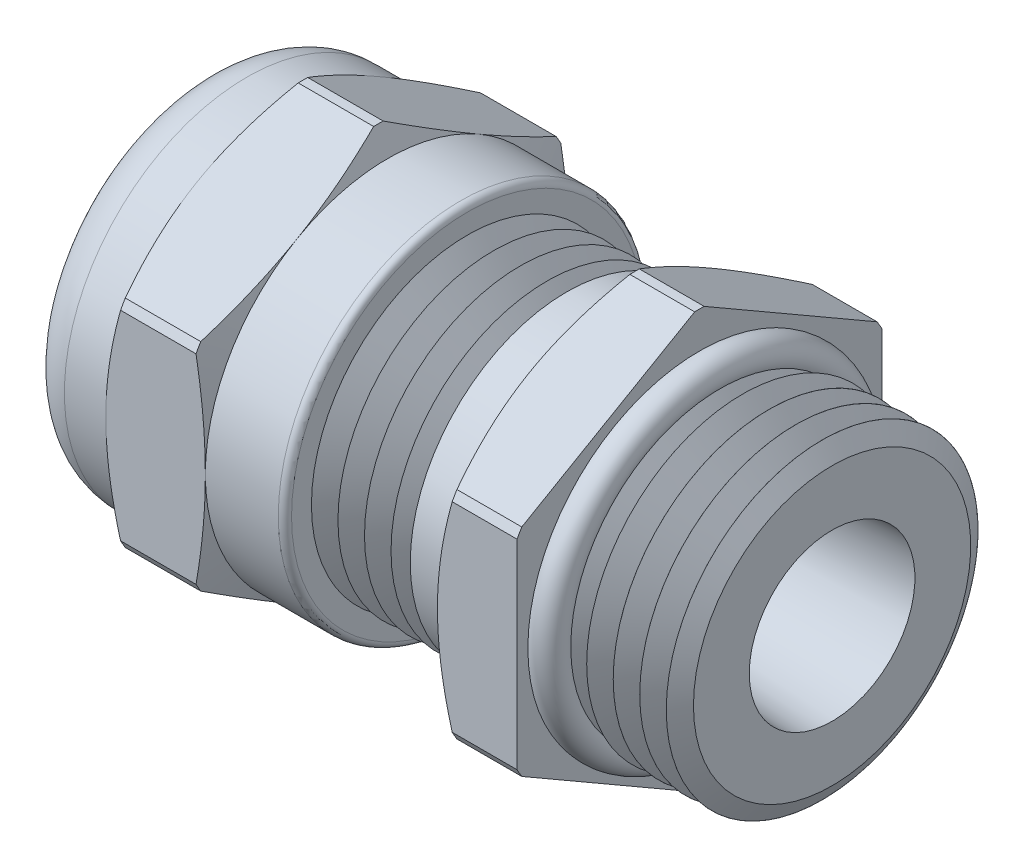
SolidWorks part; units mm, degrees
ref_plane "Front Plane" through (0, 0, 0) normal (0, 0, 1) x (1, 0, 0)
ref_plane "Top Plane" through (0, 0, 0) normal (0, 1, 0) x (1, 0, 0)
ref_plane "Right Plane" through (0, 0, 0) normal (1, 0, 0) x (0, 0, -1)
sketch "Sketch2" plane through (0, 0, 0) normal (0, 0, 1) x (1, 0, 0)
  line L0 (-69.0751, 0) -> (71.6126, 0) construction
  line L1 (-12.065, 5.0641) -> (-12.065, 6.985)
  line L2 (-12.065, 6.985) -> (-8.763, 6.985)
  line L3 (-8.763, 6.985) -> (-8.763, 7.9629)
  line L4 (-8.763, 7.9629) -> (-4.953, 7.9629)
  line L5 (0, 19.614) -> (0, -16.9655) construction
  line L6 (-4.953, 7.9629) -> (-4.953, 6.985)
  line L7 (-4.953, 6.985) -> (-1.905, 6.985)
  line L8 (-1.905, 6.985) -> (-1.905, 5.969)
  line L9 (-1.905, 5.969) -> (3.937, 5.969)
  line L10 (3.937, 5.969) -> (3.937, 7.9629)
  line L11 (3.937, 7.9629) -> (6.985, 7.9629)
  line L12 (6.985, 7.9629) -> (6.985, 5.969)
  line L13 (6.985, 5.969) -> (12.065, 5.9689)
  line L14 (12.065, 5.9689) -> (12.065, 3.1723)
  line L15 (0, 2.54) -> (-8.763, 2.54)
  line L16 (-12.065, 5.0641) -> (-8.763, 5.0641)
  line L17 (-8.763, 5.0641) -> (-8.763, 2.54)
  line L18 (0, 2.54) -> (12.065, 3.1723)
  dimension "D1" = 10.1282
  dimension "CableDia" = 5.08
  dimension "Angle" = 0.001
  dimension "D3" = 3
  dimension "B" = 19.05
  dimension "D" = 5.08
  dimension "NutWidth" = 3.81
  dimension "NutWidth1" = 3.048
  dimension "D4" = 3.302
  dimension "NPT" = 11.938
  dimension "F/F1" = 15.9258
  dimension "D5" = 3.048
  dimension "D6" = 13.97
  dimension "F/F1-" = 13.97
revolve "Revolve1" add sketch "Sketch2" angle 360 about L0
sketch "Sketch6" plane through (6.985, 0, 0) normal (1, 0, 0) x (0, 0, -1)
  line L1 (6.985, -3.8233) -> (6.985, 3.8233)
  line L2 (6.8036, 4.1375) -> (0.1814, 7.9608)
  line L3 (-0.1814, 7.9608) -> (-6.8036, 4.1375)
  line L4 (-6.985, 3.8233) -> (-6.985, -3.8233)
  line L5 (-6.8036, -4.1375) -> (-0.1814, -7.9608)
  line L6 (0.1814, -7.9608) -> (6.8036, -4.1375)
  circle A0 centre (0, 0) radius 6.985 construction
  circle A1 centre (0, 0) radius 7.9629 construction
  arc A2 (6.8036, -4.1375) -> (6.985, -3.8233) centre (0, 0) ccw
  arc A3 (-0.1814, -7.9608) -> (0.1814, -7.9608) centre (0, 0) ccw
  arc A4 (-6.985, -3.8233) -> (-6.8036, -4.1375) centre (0, 0) ccw
  arc A5 (-6.8036, 4.1375) -> (-6.985, 3.8233) centre (0, 0) ccw
  arc A6 (0.1814, 7.9608) -> (-0.1814, 7.9608) centre (0, 0) ccw
  arc A7 (6.985, 3.8233) -> (6.8036, 4.1375) centre (0, 0) ccw
  dimension "F/F1" = 13.97
extrude "Cut-Extrude2" cut sketch "Sketch6" against normal up to surface (15.748 mm away) flip side to cut up to face at (-8.763, 0, 6.985)
sketch "Sketch7" plane through (-8.763, 0, 0) normal (-1, 0, 0) x (0, 0, 1)
  line L0 (-6.985, 3.8233) -> (-6.985, 0) construction
  circle A0 centre (0, 0) radius 6.985
  dimension "D1" = 13.97
extrude "Cut-Extrude3" cut sketch "Sketch7" against normal blind 2.54 draft 60 flip side to cut
sketch "Sketch8" plane through (-4.953, 0, 0) normal (1, 0, 0) x (0, 0, -1)
  line L0 (6.985, 3.8233) -> (6.985, 0) construction
  circle A0 centre (0, 0) radius 6.985
extrude "Cut-Extrude4" cut sketch "Sketch8" against normal blind 2.54 draft 70 flip side to cut
sketch "Sketch9" plane through (3.937, 0, 0) normal (-1, 0, 0) x (0, 0, 1)
  line L0 (-0.1814, -7.9608) -> (-6.8036, -4.1375) construction
  circle A0 centre (0, 0) radius 6.985
extrude "Cut-Extrude5" cut sketch "Sketch9" against normal through all draft 60 flip side to cut
sketch "Sketch12" plane through (0, 0, 0) normal (0, 0, 1) x (1, 0, 0)
  line L0 (-8.763, 2.54) -> (-8.763, 5.0641)
  line L2 (0, 2.54) -> (-8.763, 2.54) construction
  line L3 (-8.763, 5.0641) -> (-11.303, 5.0641)
  line L4 (-8.763, 0) -> (-8.763, 6.0492) construction
  line L5 (-11.557, 4.8101) -> (-11.557, 2.54)
  line L6 (-11.557, 2.54) -> (-8.763, 2.54)
  line L8 (13.8496, 0) -> (-17.3538, 0) construction
  line L9 (-8.763, 5.0641) -> (-12.065, 5.0641) construction
  line L10 (-12.065, 5.0641) -> (-12.065, -5.0641) construction
  arc A0 (-11.303, 5.0641) -> (-11.557, 4.8101) centre (-11.303, 4.8101) ccw
  dimension "D2" = 0.254
  dimension "D1" = 0.508
revolve "Revolve3" add sketch "Sketch12" angle 360 about L8
sketch "Sketch19" [suppressed] plane through (0, 0, 0) normal (0, 0, 1) x (1, 0, 0)
  line L0 (-10.9093, 8.001) -> (-10.9093, 10.8648)
  line L1 (-10.9093, 10.8648) -> (-14.6685, 10.8648)
  line L2 (-10.9093, 10.8648) -> (-15.367, 10.8648) construction
  line L3 (-15.0495, 10.4838) -> (-15.0495, 8.001)
  line L4 (-15.0495, 8.001) -> (-10.9093, 8.001)
  line L5 (-15.367, 14.986) -> (-15.367, -14.986) construction
  line L6 (-10.9093, 0) -> (-10.9093, 12.9783) construction
  line L8 (-17.0501, 0) -> (8.8956, 0) construction
  line L9 (0, 8.001) -> (-10.9093, 8.001) construction
  arc A0 (-14.6685, 10.8648) -> (-15.0495, 10.4838) centre (-14.6685, 10.4838) ccw
  dimension "D2" = 0.381
  dimension "D1" = 0.3175
revolve "Revolve5" [suppressed] add sketch "Sketch19" angle 360 about L8
fillet "Fillet1" radius 1.7145 1 edges at (-12.065, 0, 6.985)
sketch "Sketch13" plane through (0, 0, 0) normal (0, 0, 1) x (1, 0, 0)
  line L0 (-1.905, 5.969) -> (-0.889, 5.969)
  line L1 (-1.905, -6.985) -> (-1.905, 6.985) construction
  line L2 (3.937, 5.969) -> (-1.905, 5.969) construction
  line L3 (-0.889, 5.969) -> (-1.397, 5.0891)
  line L4 (-1.397, 5.0891) -> (-1.905, 5.969)
  line L5 (-15.434, 0) -> (16.1616, 0) construction
  line L6 (-1.397, 5.9839) -> (-1.397, 5.0891) construction
  dimension "D1" = 60
  dimension "P" = 1.016
revolve "Cut-Revolve1" cut sketch "Sketch13" angle 360 about L5
pattern_linear "LPattern1" count 6 spacing 1.016 along (1, 0, 0) of "Cut-Revolve1"
sketch "Sketch14" plane through (0, 0, 0) normal (0, 0, 1) x (1, 0, 0)
  line L0 (7.62, 5.969) -> (8.636, 5.969)
  line L1 (12.065, 5.9689) -> (6.985, 5.969) construction
  line L2 (8.636, 5.969) -> (8.128, 5.0891)
  line L3 (8.128, 5.0891) -> (7.62, 5.969)
  line L5 (-13.7951, 0) -> (13.7951, 0) construction
  line L6 (12.065, 5.9689) -> (6.985, 5.969) construction
  line L7 (6.985, 7.9608) -> (6.985, 4.1375) construction
  line L8 (8.128, 5.0891) -> (8.128, 5.969) construction
  dimension "D1" = 0.635
  dimension "D3" = 60
  dimension "P" = 1.016
revolve "Cut-Revolve2" cut sketch "Sketch14" angle 360 about L5
pattern_linear "LPattern2" count 5 spacing 1.016 along (1, 0, 0) of "Cut-Revolve2"
sketch "Sketch16" plane through (3.937, 0, 0) normal (-1, 0, 0) x (0, 0, 1)
  circle A0 centre (0, 0) radius 5.969 construction
  circle A1 centre (0, 0) radius 5.969 construction
  circle A2 centre (0, 0) radius 3.1723 construction
  circle A3 centre (0, 0) radius 3.1723
  circle A4 centre (0, 0) radius 5.9944
  dimension "D1" = 0.0254
extrude "Extrude4" add sketch "Sketch16" along normal blind 2.032 from offset 0
fillet "Fillet5" radius 0.254 1 edges at (-1.905, 0, 6.985)
sketch "Sketch18" plane through (0, 0, 0) normal (0, 0, 1) x (1, 0, 0)
  line L1 (7.62, 5.969) -> (6.985, 5.969) construction
  line L2 (6.985, 7.9608) -> (6.985, 4.1375) construction
  line L3 (19.1212, 0) -> (-17.421, 0) construction
  circle A0 centre (7.1882, 5.969) radius 0.635
  dimension "D1" = 1.27
  dimension "D2" = 0.2032
revolve "Revolve4" add sketch "Sketch18" angle 360 about L3
sketch "Sketch17" plane through (0, 0, 0) normal (1, 0, 0) x (0, 0, -1)
  line L0 (0, 4.5969) -> (0, -2.0345) construction
  line L1 (-0.1397, 3.1692) -> (-0.1397, 2.8159)
  line L2 (0.1397, 3.1692) -> (0.1397, 2.8159)
  line L3 (2.6748, 1.7056) -> (2.3688, 1.529)
  line L4 (2.8145, 1.4636) -> (2.5085, 1.287)
  line L5 (2.8145, -1.4636) -> (2.5085, -1.287)
  line L6 (2.6748, -1.7056) -> (2.3688, -1.529)
  line L7 (0.1397, -3.1692) -> (0.1397, -2.8159)
  line L8 (-0.1397, -3.1692) -> (-0.1397, -2.8159)
  line L9 (-2.6748, -1.7056) -> (-2.3688, -1.529)
  line L10 (-2.8145, -1.4636) -> (-2.5085, -1.287)
  line L11 (-2.8145, 1.4636) -> (-2.5085, 1.287)
  line L12 (-2.6748, 1.7056) -> (-2.3688, 1.529)
  circle A0 centre (0, 0) radius 3.1723 construction
  arc A2 (-2.8145, -1.4636) -> (-2.6748, -1.7056) centre (0, 0) ccw
  arc A3 (-2.5085, -1.287) -> (-2.3688, -1.529) centre (0, 0) ccw construction
  arc A4 (-2.3688, 1.529) -> (-2.5085, 1.287) centre (0, 0) ccw construction
  arc A5 (0.1397, 2.8159) -> (-0.1397, 2.8159) centre (0, 0) ccw construction
  arc A6 (2.5085, 1.287) -> (2.3688, 1.529) centre (0, 0) ccw construction
  arc A7 (2.3688, -1.529) -> (2.5085, -1.287) centre (0, 0) ccw construction
  arc A8 (-0.1397, -2.8159) -> (0.1397, -2.8159) centre (0, 0) ccw construction
  arc A9 (-2.6748, 1.7056) -> (-2.8145, 1.4636) centre (0, 0) ccw
  arc A10 (0.1397, 3.1692) -> (-0.1397, 3.1692) centre (0, 0) ccw
  arc A11 (2.8145, 1.4636) -> (2.6748, 1.7056) centre (0, 0) ccw
  arc A12 (2.6748, -1.7056) -> (2.8145, -1.4636) centre (0, 0) ccw
  arc A13 (-0.1397, -3.1692) -> (0.1397, -3.1692) centre (0, 0) ccw
  circle A16 centre (0, 0) radius 2.54 construction
  arc A17 (-2.5085, 1.287) -> (-2.5085, -1.287) centre (0, 0) ccw
  arc A18 (-0.1397, 2.8159) -> (-2.3688, 1.529) centre (0, 0) ccw
  arc A19 (2.3688, 1.529) -> (0.1397, 2.8159) centre (0, 0) ccw
  arc A20 (2.5085, -1.287) -> (2.5085, 1.287) centre (0, 0) ccw
  arc A21 (0.1397, -2.8159) -> (2.3688, -1.529) centre (0, 0) ccw
  arc A22 (-2.3688, -1.529) -> (-0.1397, -2.8159) centre (0, 0) ccw
  circle A23 centre (0, 0) radius 2.54
  dimension "D2" = 0.2794
  dimension "D1" = 0.2794
equation "\"F/F1-@Sketch2\" = \"D6@Sketch2\""
equation "\"D1@Sketch2\" = \"F/F1-@Sketch2\"*0.725"
equation "\"D2@Sketch17\" = \"CableDia@Sketch2\"*0.055"
equation "\"D1@Sketch17\" = \"D2@Sketch17\""
